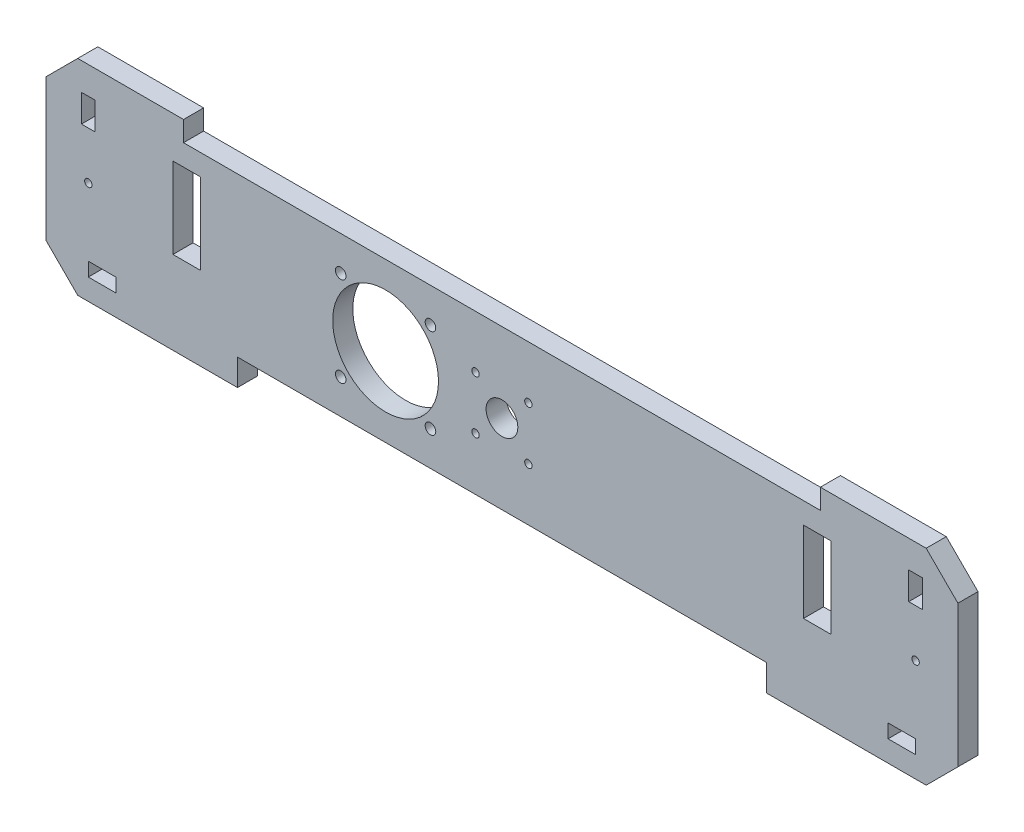
SolidWorks part; units mm, degrees
ref_plane "Alzado" through (0, 0, 0) normal (0, 0, 1) x (1, 0, 0)
ref_plane "Planta" through (0, 0, 0) normal (0, 1, 0) x (1, 0, 0)
ref_plane "Vista lateral" through (0, 0, 0) normal (1, 0, 0) x (0, 0, -1)
sketch "Croquis1" plane through (0, 0, 0) normal (0, 0, 1) x (1, 0, 0)
  line L0 (-301, 194) -> (-301, 175)
  line L1 (-250, 25) -> (250, 25)
  line L2 (250, 25) -> (250, 0)
  line L3 (250, 0) -> (401, 0)
  line L4 (401, 0) -> (431, 30)
  line L5 (431, 30) -> (431, 164)
  line L6 (431, 164) -> (401, 194)
  line L7 (401, 194) -> (301, 194)
  line L8 (301, 194) -> (301, 175)
  line L9 (301, 175) -> (-301, 175)
  line L10 (-401, 194) -> (-301, 194)
  line L11 (-431, 164) -> (-401, 194)
  line L12 (-431, 30) -> (-431, 164)
  line L13 (0, 0) -> (0, 25) construction
  line L14 (0, 25) -> (0, 175) construction
  line L15 (-401, 0) -> (-431, 30)
  line L16 (-250, 0) -> (-401, 0)
  line L17 (-250, 25) -> (-250, 0)
  line L18 (-391, 0) -> (-391, 97) construction
  line L19 (-311, 155) -> (-285, 155)
  line L20 (-311, 155) -> (-311, 78.5)
  line L21 (-311, 78.5) -> (-285, 78.5)
  line L22 (-285, 155) -> (-285, 78.5)
  line L23 (-311, 155) -> (-285, 78.5) construction
  line L24 (-311, 78.5) -> (-285, 155) construction
  line L25 (-391, 97) -> (-391, 194) construction
  line L26 (311, 78.5) -> (285, 78.5)
  line L27 (311, 155) -> (311, 78.5)
  line L28 (311, 155) -> (285, 155)
  line L29 (285, 155) -> (285, 78.5)
  line L30 (-110, 175) -> (-110, 100) construction
  line L31 (25, 75) -> (-25, 75) construction
  line L32 (25, 75) -> (25, 125) construction
  line L33 (25, 125) -> (-25, 125) construction
  line L34 (-25, 75) -> (-25, 125) construction
  line L35 (25, 75) -> (-25, 125) construction
  line L36 (25, 125) -> (-25, 75) construction
  line L37 (-110, 100) -> (-110, 25) construction
  line L38 (-110, 100) -> (-152.4264, 142.4264) construction
  line L39 (-67.5736, 142.4264) -> (-110, 100) construction
  line L40 (-110, 100) -> (-152.4264, 57.5736) construction
  line L41 (391, 33) -> (391, 20)
  line L42 (-67.5736, 57.5736) -> (-110, 100) construction
  line L43 (-365, 33) -> (-391, 33)
  line L44 (-365, 33) -> (-365, 20)
  line L45 (-365, 20) -> (-391, 20)
  line L46 (-391, 33) -> (-391, 20)
  line L47 (-365, 33) -> (-391, 20) construction
  line L48 (-365, 20) -> (-391, 33) construction
  line L49 (365, 20) -> (391, 20)
  line L50 (365, 33) -> (365, 20)
  line L51 (365, 33) -> (391, 33)
  line L52 (397.5, 168) -> (397.5, 142)
  line L53 (-397.5, 168) -> (-384.5, 168)
  line L54 (-397.5, 168) -> (-397.5, 142)
  line L55 (-397.5, 142) -> (-384.5, 142)
  line L56 (-384.5, 168) -> (-384.5, 142)
  line L57 (-397.5, 168) -> (-384.5, 142) construction
  line L58 (-397.5, 142) -> (-384.5, 168) construction
  line L59 (397.5, 168) -> (384.5, 168)
  line L60 (384.5, 168) -> (384.5, 142)
  line L61 (397.5, 142) -> (384.5, 142)
  circle A0 centre (-391, 97) radius 3.5
  circle A1 centre (391, 97) radius 3.5
  circle A2 centre (0, 100) radius 15
  circle A3 centre (-25, 125) radius 3.5
  circle A4 centre (25, 125) radius 3.5
  circle A5 centre (25, 75) radius 3.5
  circle A6 centre (-25, 75) radius 3.5
  circle A7 centre (-110, 100) radius 50
  circle A8 centre (-152.4264, 142.4264) radius 5
  circle A9 centre (-67.5736, 142.4264) radius 5
  circle A10 centre (-67.5736, 57.5736) radius 5
  circle A11 centre (-152.4264, 57.5736) radius 5
  point P20 (-298, 116.75)
  point P57 (-378, 26.5)
  point P66 (-391, 155)
  dimension "D14" = 40
  dimension "D15" = 7
  dimension "D16" = 30
  dimension "D17" = 7
  dimension "D20" = 100
  dimension "D22" = 45
  dimension "D26" = 10
  dimension "D1" = 150
  dimension "D2" = 301
  dimension "D3" = 100
  dimension "D4" = 19
  dimension "D5" = 135
  dimension "D6" = 30
  dimension "D7" = 25
  dimension "D8" = 250
  dimension "D9" = 30
  dimension "D10" = 76.5
  dimension "D11" = 26
  dimension "D12" = 10
  dimension "D13" = 20
  dimension "D18" = 50
  dimension "D19" = 50
  dimension "D21" = 110
  dimension "D23" = 45
  dimension "D24" = 45
  dimension "D25" = 45
  dimension "D27" = 60
  dimension "D28" = 60
  dimension "D29" = 60
  dimension "D30" = 60
  dimension "D31" = 26
  dimension "D32" = 13
  dimension "D33" = 20
  dimension "D34" = 40
  dimension "D35" = 26
  dimension "D36" = 194
  dimension "D37" = 862
extrude "Saliente-Extruir1" add sketch "Croquis1" along normal blind 19
